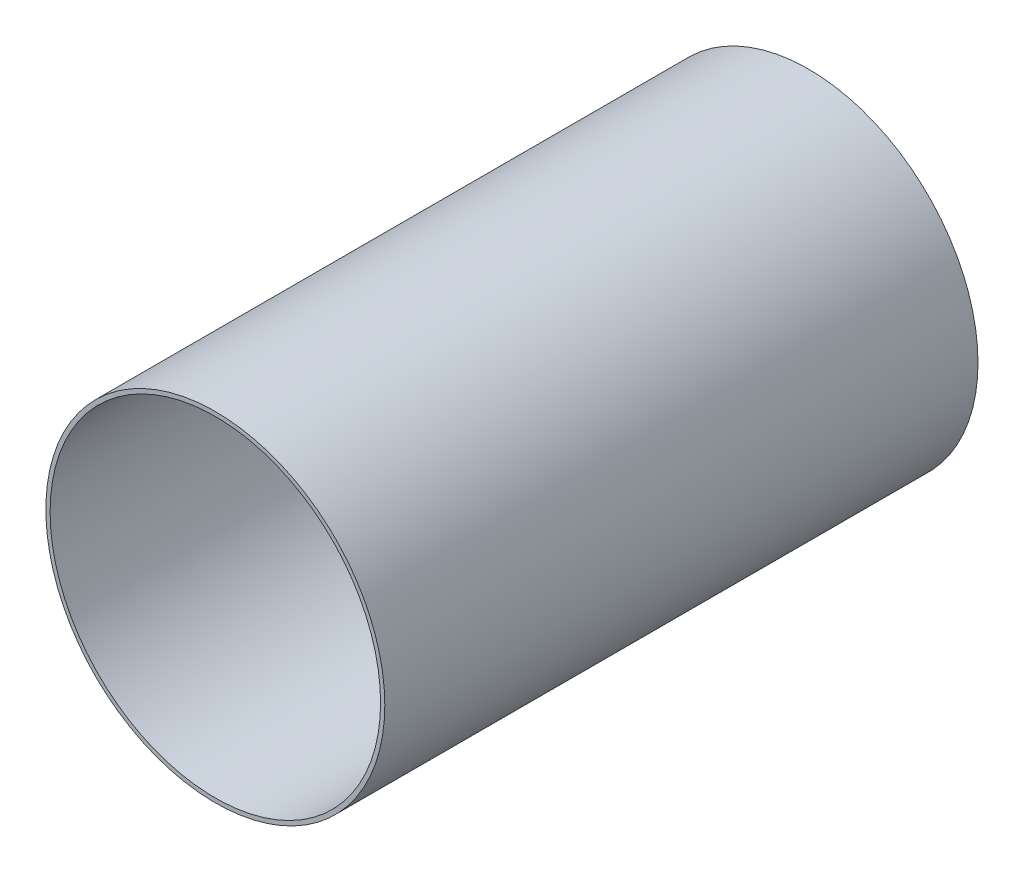
SolidWorks part; units mm, degrees
ref_plane "Front Plane" through (0, 0, 0) normal (0, 0, 1) x (1, 0, 0)
ref_plane "Top Plane" through (0, 0, 0) normal (0, 1, 0) x (1, 0, 0)
ref_plane "Right Plane" through (0, 0, 0) normal (1, 0, 0) x (0, 0, -1)
sketch "Sketch1" plane through (0, 0, 0) normal (0, 0, 1) x (1, 0, 0)
  circle A0 centre (0, 40) radius 20
  circle A1 centre (0, 40) radius 19.5
  dimension "D1" = 40
  dimension "D2" = 39
extrude "Boss-Extrude1" add sketch "Sketch1" along normal blind 70
